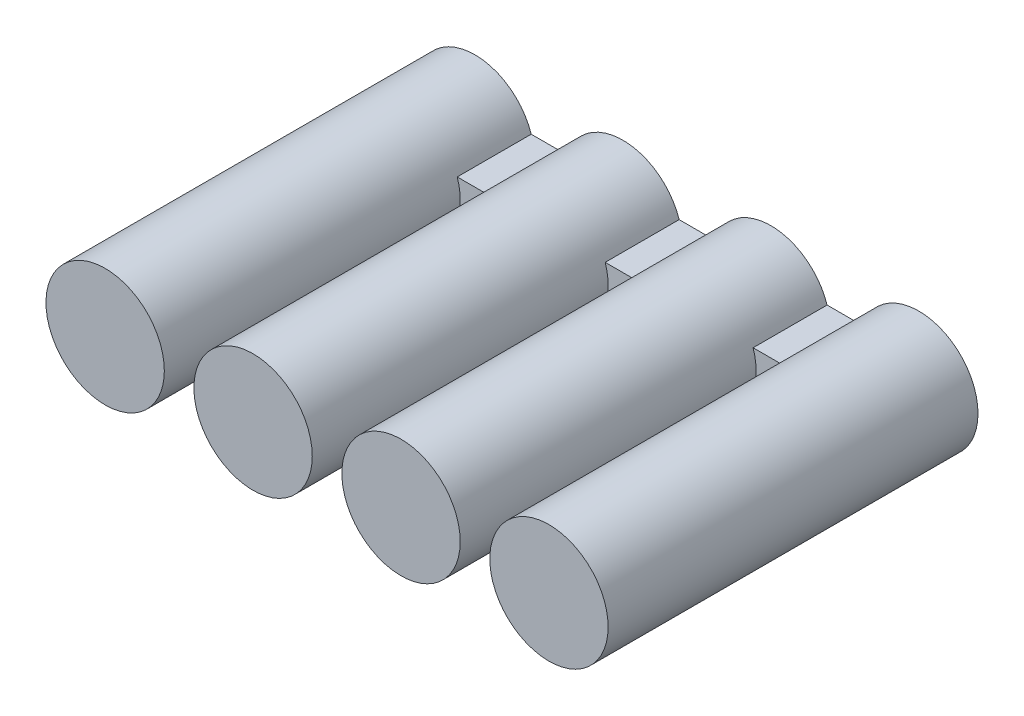
SolidWorks part; units mm, degrees
ref_plane "Plano frontal" through (0, 0, 0) normal (0, 0, 1) x (1, 0, 0)
ref_plane "Plano superior" through (0, 0, 0) normal (0, 1, 0) x (1, 0, 0)
ref_plane "Plano direito" through (0, 0, 0) normal (1, 0, 0) x (0, 0, -1)
sketch "Esboço1" plane through (0, 0, 0) normal (0, 0, 1) x (1, 0, 0)
  circle A0 centre (-3.5021, 1.3793) radius 0.8
  circle A1 centre (-1.5021, 1.3793) radius 0.8
  circle A2 centre (0.4979, 1.3793) radius 0.8
  circle A3 centre (2.4979, 1.3793) radius 0.8
  dimension "D1" = 1.6
  dimension "D2" = 2
  dimension "D3" = 2
  dimension "D4" = 2
  dimension "D5" = 0
  dimension "D6" = 0
  dimension "D7" = 0
extrude "Ressalto-extrusão1" add sketch "Esboço1" along normal blind 5
sketch "Esboço2" plane through (0, 0, 0) normal (0, 0, -1) x (-1, 0, 0)
  line L0 (-1.9979, 1.3793) -> (3.0021, 1.3793) construction
  line L1 (-1.9979, 1.6293) -> (3.0021, 1.6293)
  line L2 (-1.9979, 1.6293) -> (-1.9979, 1.1293)
  line L3 (-1.9979, 1.1293) -> (3.0021, 1.1293)
  line L4 (3.0021, 1.6293) -> (3.0021, 1.1293)
  circle A0 centre (-2.4979, 1.3793) radius 0.8 construction
  circle A1 centre (-2.4979, 1.3793) radius 0.8
  circle A2 centre (3.5021, 1.3793) radius 0.8 construction
  circle A3 centre (3.5021, 1.3793) radius 0.8
  circle M4 centre (-2.4979, 1.3793) radius 0.8
  dimension "D1" = 5
  dimension "D2" = 0.5
  dimension "D3" = 0.5
  dimension "D4" = 0
extrude "Ressalto-extrusão2" add sketch "Esboço2" against normal blind 1 contours L0 L3 A3 M4 | A1 L0 A3 L1
